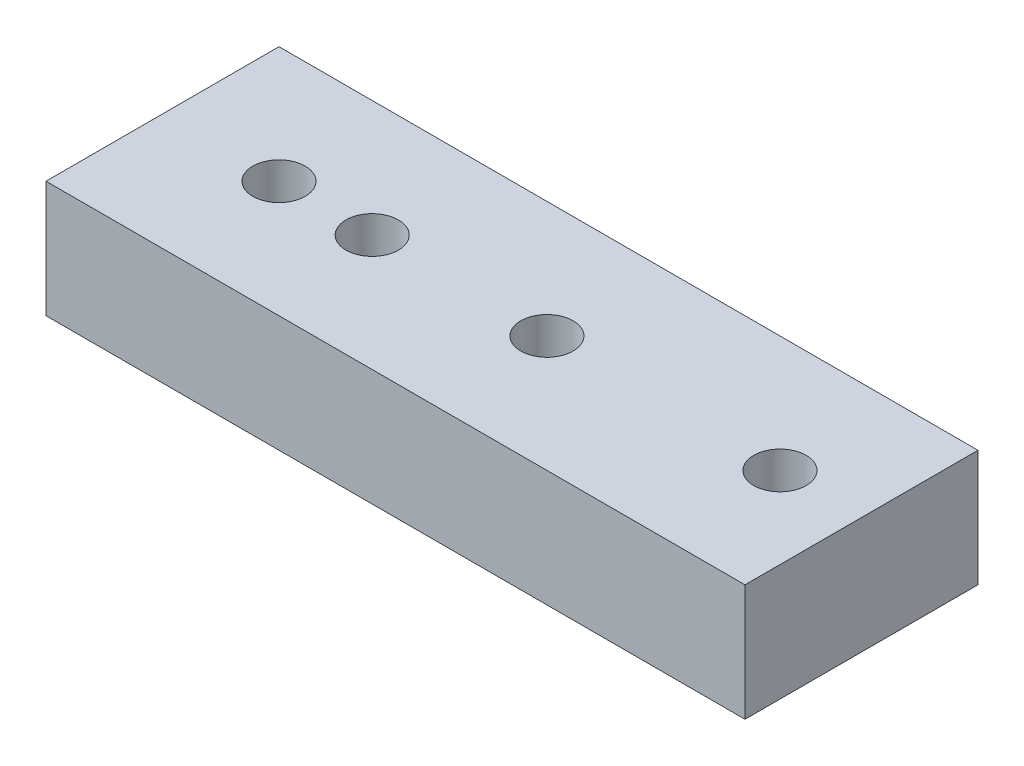
SolidWorks part; units mm, degrees
ref_plane "Front Plane" through (0, 0, 0) normal (0, 0, 1) x (1, 0, 0)
ref_plane "Top Plane" through (0, 0, 0) normal (0, 1, 0) x (1, 0, 0)
ref_plane "Right Plane" through (0, 0, 0) normal (1, 0, 0) x (0, 0, -1)
sketch "Sketch1" plane through (0, 0, 0) normal (0, 1, 0) x (1, 0, 0)
  line L1 (-18, 10) -> (42, 10)
  line L2 (-18, 10) -> (-18, -10)
  line L3 (-18, -10) -> (42, -10)
  line L4 (42, 10) -> (42, -10)
  circle A0 centre (0, 0) radius 2.25
  circle A1 centre (-8, 0) radius 2.25
  circle A2 centre (35, 0) radius 2.25
  circle A3 centre (15, 0) radius 2.25
  point P9 (-18, 0)
  point P14 (0, 0)
  dimension "D1" = 4.5
  dimension "D6" = 7
  dimension "D7" = 15
  dimension "D2" = 8
  dimension "D3" = 20
  dimension "D4" = 10
  dimension "D5" = 60
extrude "Boss-Extrude1" add sketch "Sketch1" along normal blind 10
sketch "Sketch2" plane through (0, 0, 0) normal (0, -1, 0) x (1, 0, 0)
  line L0 (-18, -10) -> (-18, 10) construction
  line L1 (-3.5, 2.0207) -> (-3.5, -2.0207)
  line L2 (-3.5, -2.0207) -> (0, -4.0415)
  line L3 (0, -4.0415) -> (3.5, -2.0207)
  line L4 (3.5, -2.0207) -> (3.5, 2.0207)
  line L5 (3.5, 2.0207) -> (0, 4.0415)
  line L6 (0, 4.0415) -> (-3.5, 2.0207)
  line L7 (-4.5, 2.0207) -> (-8, 4.0415)
  line L8 (-8, 4.0415) -> (-11.5, 2.0207)
  line L9 (-11.5, 2.0207) -> (-11.5, -2.0207)
  line L10 (-11.5, -2.0207) -> (-8, -4.0415)
  line L11 (-8, -4.0415) -> (-4.5, -2.0207)
  line L12 (-4.5, -2.0207) -> (-4.5, 2.0207)
  circle A0 centre (0, 0) radius 3.5 construction
  circle A1 centre (-8, 0) radius 3.5 construction
  dimension "D1" = 7
extrude "Cut-Extrude1" cut sketch "Sketch2" against normal blind 3.2
